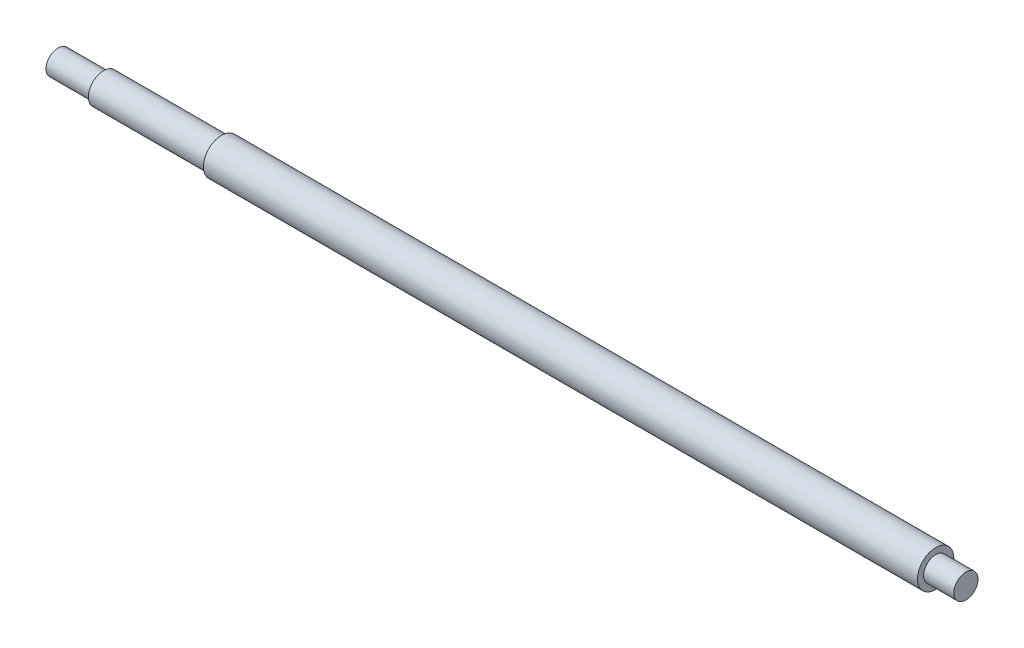
SolidWorks part; units mm, degrees
material "不锈钢 (铁素体)"
ref_plane "前视基准面" through (0, 0, 0) normal (0, 0, 1) x (1, 0, 0)
ref_plane "上视基准面" through (0, 0, 0) normal (0, 1, 0) x (1, 0, 0)
ref_plane "右视基准面" through (0, 0, 0) normal (1, 0, 0) x (0, 0, -1)
sketch "草图1" plane through (0, 0, 0) normal (0, 0, 1) x (1, 0, 0)
  line L0 (0, 0) -> (340.1938, 0) construction
  line L1 (0, 0) -> (0, 4)
  line L2 (0, 4) -> (15, 4)
  line L3 (15, 4) -> (15, 5)
  line L4 (15, 5) -> (54, 5)
  line L5 (54, 5) -> (54, 6)
  line L6 (54, 6) -> (290, 6)
  line L7 (290, 6) -> (290, 4)
  line L8 (290, 4) -> (300, 4)
  line L9 (300, 4) -> (300, 0)
  line L10 (0, 0) -> (300, 0)
  dimension "D1" = 4
  dimension "D2" = 15
  dimension "D3" = 5
  dimension "D4" = 39
  dimension "D5" = 4
  dimension "D6" = 6
  dimension "D7" = 10
  dimension "D8" = 300
revolve "旋转1" add sketch "草图1" angle 360 about L0
